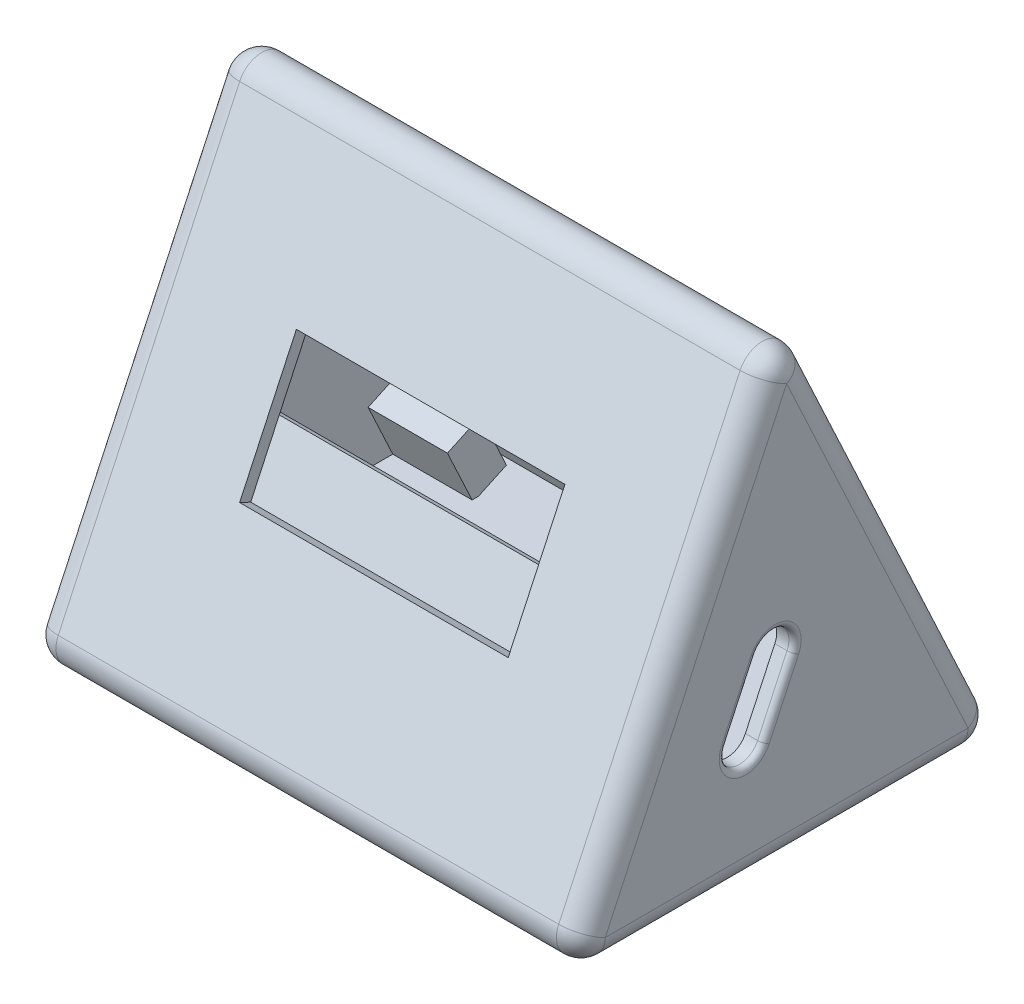
SolidWorks part; units mm, degrees
ref_plane "前视基准面" through (0, 0, 0) normal (0, 0, 1) x (1, 0, 0)
ref_plane "上视基准面" through (0, 0, 0) normal (0, 1, 0) x (1, 0, 0)
ref_plane "右视基准面" through (0, 0, 0) normal (1, 0, 0) x (0, 0, -1)
sketch "草图1" plane through (0, 0, 0) normal (1, 0, 0) x (0, 0, -1)
  line L0 (0, 0) -> (0, 38.6011) construction
  line L1 (18, 0) -> (-18, 0)
  line L2 (-18, 0) -> (0, 38.6011)
  line L3 (18, 0) -> (0, 38.6011)
  dimension "D1" = 18
  dimension "D2" = 65
extrude "凸台-拉伸1" add sketch "草图1" along normal mid plane 45
ref_plane "基准面1" through (0, 6.8944, 14.7851) normal (0, 0.4226, 0.9063) x (1, 0, 0)
sketch "草图2" plane through (0, 6.8944, 14.7851) normal (0, 0.4226, 0.9063) x (1, 0, 0)
  line L0 (0, 37.0396) -> (0, -15.9465) construction
  line L1 (-28.8471, 13.7138) -> (32.5804, 13.7138) construction
  line L2 (-11, 8.2138) -> (11, 8.2138)
  line L3 (11, 8.2138) -> (11, 19.2138)
  line L4 (-11, 19.2138) -> (11, 19.2138)
  line L5 (-11, 8.2138) -> (-11, 19.2138)
  point P9 (11, 13.7138)
  point P11 (0, 8.2138)
  point P12 (0, 19.2138)
  dimension "D1" = 11
  dimension "D2" = 5.5
extrude "切除-拉伸1" cut sketch "草图2" against normal blind 1
ref_plane "基准面2" through (0, 6.4718, 13.8788) normal (0, 0.4226, 0.9063) x (1, 0, 0)
sketch "草图3" plane through (0, 6.4718, 13.8788) normal (0, 0.4226, 0.9063) x (1, 0, 0)
  line L0 (0, 19.8103) -> (0, 5.2367) construction
  line L1 (14, 13.6867) -> (-13.0702, 13.6867) construction
  line L2 (0, 5.2367) -> (14, 5.2367)
  line L3 (14, 5.2367) -> (14, 13.6867)
  line L4 (0, 5.2367) -> (-21, 5.2367)
  line L5 (-21, 5.2367) -> (-21, 28.3584)
  line L6 (-21, 28.3584) -> (14, 28.3584)
  line L7 (14, 28.3584) -> (14, 13.6867)
  line L8 (-22.5, 34.9845) -> (-22.5, -7.6071) construction
  dimension "D1" = 14
  dimension "D2" = 8.45
  dimension "D3" = 1.5
extrude "切除-拉伸2" cut sketch "草图3" against normal blind 1.5
sketch "草图4" plane through (0, 0, 0) normal (1, 0, 0) x (0, 0, -1)
  line L0 (0, 40.4929) -> (0, -2.5128) construction
  line L1 (0.8275, 33.2772) -> (-13.9904, 1.5)
  line L2 (-13.9904, 1.5) -> (15.6455, 1.5)
  line L3 (15.6455, 1.5) -> (0.8275, 33.2772)
  line L4 (0, 38.6011) -> (-18, 0) construction
  line L5 (-18, 0) -> (18, 0) construction
  line L7 (18, 0) -> (0, 38.6011) construction
  dimension "D1" = 3
  dimension "D2" = 1.5
  dimension "D3" = 1.5
extrude "切除-拉伸3" cut sketch "草图4" against normal mid plane 42
ref_plane "基准面3" through (0, 6.8944, -14.7851) normal (0, 0.4226, -0.9063) x (-1, 0, 0)
sketch "草图5" plane through (0, 6.8944, -14.7851) normal (0, 0.4226, -0.9063) x (-1, 0, 0)
  line L0 (0, 37.0585) -> (0, -12.822) construction
  line L1 (-24.7953, 13.7133) -> (25.2303, 13.7133) construction
  line L2 (19.5, -3.6071) -> (-19.5, -3.6071)
  line L3 (-19.5, -3.6071) -> (-19.5, 26.9845)
  line L4 (-19.5, 26.9845) -> (19.5, 26.9845)
  line L5 (-22.5, -7.6071) -> (22.5, -7.6071) construction
  line L6 (-22.5, -7.6071) -> (-22.5, 34.9845) construction
  line L7 (-22.5, 34.9845) -> (22.5, 34.9845) construction
  line L8 (19.5, -3.6071) -> (19.5, 26.9845)
  point P17 (0, -3.6071)
  point P18 (0, 26.9845)
  dimension "D1" = 4
  dimension "D2" = 3
  dimension "D3" = 8
extrude "切除-拉伸4" cut sketch "草图5" against normal blind 1.5
ref_plane "基准面4" through (0, 5.6265, 12.0662) normal (0, -0.4226, -0.9063) x (-1, 0, 0)
sketch "草图6" plane through (0, 5.6265, 12.0662) normal (0, -0.4226, -0.9063) x (-1, 0, 0)
  line L0 (-21, 13.2048) -> (14.1537, 13.2048)
  line L1 (14.1537, 13.2048) -> (14.1537, 10.3593)
  line L2 (14.1537, 10.3593) -> (21, 10.3593)
  line L3 (21, 10.3593) -> (21, 29.9845)
  line L4 (21, 29.9845) -> (-21, 29.9845)
  line L5 (-21, 29.9845) -> (-21, 13.2048)
  line L6 (22.5, 34.9845) -> (22.5, -7.6071) construction
  line L7 (-22.5, 34.9845) -> (22.5, 34.9845) construction
  line L8 (-22.5, 34.9845) -> (-22.5, -7.6071) construction
  dimension "D1" = 1.5
  dimension "D2" = 5
  dimension "D3" = 1.5
extrude "切除-拉伸5" cut sketch "草图6" against normal blind 2
ref_plane "基准面6" through (0, 4.5277, 9.7098) normal (0, -0.4226, -0.9063) x (-1, 0, 0)
sketch "草图9" plane through (0, 4.5277, 9.7098) normal (0, -0.4226, -0.9063) x (-1, 0, 0)
  line L0 (-19.9951, -2.98) -> (-19.9951, 22.2211) construction
  line L1 (-19.9951, 22.2211) -> (19.0049, 22.2211) construction
  line L2 (19.0049, 22.2211) -> (19.0049, -2.98) construction
  line L3 (19.0049, -2.98) -> (-19.9951, -2.98) construction
  line L4 (-22.4951, 30.2673) -> (-22.4951, -4.98) construction
  line L5 (-22.4951, -4.98) -> (22.5177, -4.98) construction
  line L6 (-19.9951, 22.2211) -> (-15.9951, 22.2211)
  line L7 (-15.9951, 22.2211) -> (-15.9951, 18.2211)
  line L8 (-15.9951, 18.2211) -> (-19.9951, 18.2211)
  line L9 (-19.9951, 18.2211) -> (-19.9951, 22.2211)
  line L10 (9.6049, 1.6211) -> (13.6049, 1.6211)
  line L11 (13.6049, 1.6211) -> (13.6049, -2.3789)
  line L12 (13.6049, -2.3789) -> (9.6049, -2.3789)
  line L13 (9.6049, -2.3789) -> (9.6049, 1.6211)
  line L16 (-19.9951, 22.2211) -> (-20.0443, 22.2112) construction
  line L19 (13.6049, -2.3789) -> (13.6019, -2.3862) construction
  dimension "D1" = 2.5
  dimension "D2" = 39
  dimension "D3" = 2
  dimension "D4" = 4
  dimension "D5" = 4
  dimension "D6" = 4
  dimension "D7" = 4
  dimension "D8" = 16.6
  dimension "D9" = 25.6
extrude "凸台-拉伸2" add sketch "草图9" against normal blind 5
sketch "草图10" plane through (0, 4.5277, 9.7098) normal (0, -0.4226, -0.9063) x (-1, 0, 0)
  line L0 (-15.9951, 22.2211) -> (-19.9951, 18.2211) construction
  line L1 (-19.9951, 22.2211) -> (-15.9951, 18.2211) construction
sketch "草图11" plane through (0, 4.5277, 9.7098) normal (0, -0.4226, -0.9063) x (-1, 0, 0)
  line L0 (13.6049, 1.6211) -> (9.6049, -2.3789) construction
  line L1 (9.6049, 1.6211) -> (13.6049, -2.3789) construction
sketch "草图12" plane through (22.5, 0, 0) normal (1, 0, 0) x (0, 0, -1)
  line L2 (-1.164, 22.8542) -> (-5.3056, 13.9724) construction
  line L3 (-4.8583, 14.9317) -> (-3.227, 14.1709) construction
  line L4 (-3.227, 14.1709) -> (-4.9545, 10.4663) construction
  line L5 (-5.3056, 13.9724) -> (1.2067, 10.9357) construction
  line L6 (-3.3734, 9.938) -> (-0.9644, 15.1039) construction
  line L7 (-4.8688, 10.6353) -> (-2.4598, 15.8013)
  line L8 (-1.878, 9.2407) -> (0.531, 14.4066)
  line L9 (-17.5905, -12.3726) -> (-1.829, 21.4281) construction
  arc A0 (-4.8688, 10.6353) -> (-1.878, 9.2407) centre (-3.3734, 9.938) ccw
  arc A1 (0.531, 14.4066) -> (-2.4598, 15.8013) centre (-0.9644, 15.1039) ccw
  point P10 (-2.1689, 12.521)
  point P17 (-4.0707, 8.4426)
  point P18 (-0.2671, 16.5994)
  dimension "D1" = 9.8
  dimension "D2" = 1.8
  dimension "D3" = 3.3
  dimension "D4" = 9
extrude "切除-拉伸6" cut sketch "草图12" against normal blind 5
sketch "草图14" plane through (-22.5, 0, 0) normal (-1, 0, 0) x (0, 0, 1)
  line L4 (-1.12, 30.2837) -> (-3.2331, 25.7522)
  line L5 (-3.2331, 25.7522) -> (-0.5142, 24.4843)
  line L6 (-0.5142, 24.4843) -> (1.5989, 29.0158)
  line L7 (1.5989, 29.0158) -> (-1.12, 30.2837)
  dimension "D2" = 5
  dimension "D3" = 3
extrude "凸台-拉伸3" add sketch "草图14" against normal blind 8
sketch "草图15" plane through (22.5, 0, 0) normal (1, 0, 0) x (0, 0, -1)
  line L4 (14.0438, 2.5687) -> (11.3248, 1.3008)
  line L5 (11.3248, 1.3008) -> (9.2117, 5.8324)
  line L6 (9.2117, 5.8324) -> (11.9307, 7.1002)
  line L7 (11.9307, 7.1002) -> (14.0438, 2.5687)
  dimension "D2" = 5
  dimension "D3" = 3
extrude "凸台-拉伸4" add sketch "草图15" against normal blind 8
sketch "草图18" plane through (0, 5.8379, -12.5193) normal (0, 0.4226, -0.9063) x (-1, 0, 0)
  line L0 (19.5, 26.9845) -> (14.5, 21.973) construction
  line L1 (14.5, 26.973) -> (19.5, 21.973) construction
  line L2 (14.5, 21.973) -> (21, 21.973) construction
  line L3 (19.5, -3.6071) -> (19.5, 26.9845) construction
sketch "草图19" plane through (0, 5.8379, -12.5193) normal (0, 0.4226, -0.9063) x (-1, 0, 0)
  line L0 (-19.5, 1.3929) -> (-14.5, -3.6071) construction
  line L1 (-19.5, 26.9845) -> (-19.5, -3.6071) construction
  line L2 (-14.5, 1.3929) -> (-21, 1.3929) construction
  line L3 (-14.5, 1.3929) -> (-19.5, -3.6071) construction
hole_wizard "M2 螺纹孔3" positions "3D草图4" profile "草图21" tap size "M2" standard "GB"
sketch3d "3D草图4"
  line L0 (-19.5, 30.2941, -1.1152) -> (-14.5, 25.7522, -3.2331) construction
  line L1 (19.5, 7.1002, -11.9307) -> (14.5, 2.5687, -14.0438) construction
  point P0 (17, 4.8345, -12.9872)
  point P2 (-17, 28.0231, -2.1742)
sketch "草图21" plane through (17, 4.8345, -12.9872) normal (1, 0, 0) x (0, 0.9063, 0.4226)
  line L0 (0, 0) -> (0, 2.9807)
  line L1 (0, 2.9807) -> (0.8, 2.5)
  line L2 (0.8, 2.5) -> (0.8, 0)
  line L5 (0.8, 0) -> (0, 0)
  line L10 (0, 2.9807) -> (-0.8, 2.5) construction
  line L11 (0, -6.35) -> (0, 107.95) construction
  dimension "螺纹孔钻头直径" = 1.6
  dimension "螺纹孔钻头深度" = 2.5
  dimension "导头角度" = 118
cosmetic thread "孔螺蚊线7" parameters "D1"=2.3, "D2"=2
cosmetic thread "孔螺蚊线8" parameters "D1"=2.3, "D2"=2
hole_wizard "M2 螺纹孔5" positions "3D草图6" profile "草图23" tap size "M2" standard "GB"
sketch3d "3D草图6"
  line L0 (15.9951, 24.6669, 0.3187) -> (19.9951, 21.0416, 2.0092) construction
  point P0 (17.9951, 22.8542, 1.164)
  point P5 (17.9951, 22.8542, 1.164)
  point P6 (17.9951, 22.8542, 1.164)
sketch "草图23" plane through (17.9951, 22.8542, 1.164) normal (1, 0, 0) x (0, 0.9063, -0.4226)
  line L0 (0, 0) -> (0, 2.9807)
  line L1 (0, 2.9807) -> (0.8, 2.5)
  line L2 (0.8, 2.5) -> (0.8, 0)
  line L5 (0.8, 0) -> (0, 0)
  line L10 (0, 2.9807) -> (-0.8, 2.5) construction
  line L11 (0, -6.35) -> (0, 107.95) construction
  dimension "螺纹孔钻头直径" = 1.6
  dimension "螺纹孔钻头深度" = 2.5
  dimension "导头角度" = 118
cosmetic thread "孔螺蚊线11" parameters "D1"=2.3, "D2"=2
cosmetic thread "孔螺蚊线12" parameters "D1"=2.3, "D2"=2
ref_plane "基准面7" through (0, 0, 9) normal (0, 0, 1) x (1, 0, 0)
sketch "草图27" plane through (-22.5, 0, 0) normal (-1, 0, 0) x (0, 0, 1)
  line L4 (-14.9501, 2.9913) -> (-12.2711, 1.7421) construction
  line L5 (-14.0438, 2.5687) -> (-11.9307, 7.1002)
  line L6 (-11.9307, 7.1002) -> (-9.2117, 5.8324)
  line L7 (-9.2117, 5.8324) -> (-11.3248, 1.3008)
  line L8 (-11.3248, 1.3008) -> (-14.0438, 2.5687)
  dimension "D2" = 3
  dimension "D3" = 5
extrude "凸台-拉伸6" add sketch "草图27" against normal blind 8
sketch "草图28" plane through (22.5, 0, 0) normal (1, 0, 0) x (0, 0, -1)
  line L4 (2.0215, 30.7167) -> (-1.2539, 29.1894) construction
  line L5 (1.1152, 30.2941) -> (-1.6037, 29.0263)
  line L6 (-1.6037, 29.0263) -> (0.5093, 24.4947)
  line L7 (0.5093, 24.4947) -> (3.2283, 25.7626)
  line L9 (1.1152, 30.2941) -> (3.2283, 25.7626)
  dimension "D2" = 5
  dimension "D3" = 3
extrude "凸台-拉伸7" add sketch "草图28" against normal blind 8
sketch "草图29" plane through (0, 5.8379, -12.5193) normal (0, 0.4226, -0.9063) x (-1, 0, 0)
  line L0 (-14.5, 21.9845) -> (-19.5, 26.9845) construction
  line L1 (-14.5, 26.9845) -> (-19.5, 21.9845) construction
  line L2 (-19.5, 26.9845) -> (-19.5, -3.6071) construction
  line L3 (-14.5, 21.9845) -> (-21, 21.9845) construction
sketch "草图31" plane through (0, 5.8379, -12.5193) normal (0, 0.4226, -0.9063) x (-1, 0, 0)
  line L0 (19.5, -3.6071) -> (14.5, 1.3929) construction
  line L1 (14.5, 1.3929) -> (14.5, -3.6071) construction
  line L2 (19.5, 1.3929) -> (14.5, -3.6071) construction
  line L3 (14.5, 1.3929) -> (21, 1.3929) construction
  line L4 (19.5, -3.6071) -> (19.5, 26.9845) construction
hole_wizard "M2 螺纹孔7" positions "3D草图8" profile "草图32" tap size "M2" standard "GB"
sketch3d "3D草图8"
  line L0 (14.5, 25.7626, -3.2283) -> (19.5, 30.2941, -1.1152) construction
  line L1 (-19.5, 2.5687, -14.0438) -> (-14.5, 7.1002, -11.9307) construction
  point P0 (17, 28.0283, -2.1717)
  point P2 (-17, 4.8345, -12.9872)
  point P3 (17, 28.0283, -2.1717)
  point P6 (-17, 4.8345, -12.9872)
sketch "草图32" plane through (17, 28.0283, -2.1717) normal (1, 0, 0) x (0, 0.9063, 0.4226)
  line L0 (0, 0) -> (0, 2.9807)
  line L1 (0, 2.9807) -> (0.8, 2.5)
  line L2 (0.8, 2.5) -> (0.8, 0)
  line L5 (0.8, 0) -> (0, 0)
  line L10 (0, 2.9807) -> (-0.8, 2.5) construction
  line L11 (0, -6.35) -> (0, 107.95) construction
  dimension "螺纹孔钻头直径" = 1.6
  dimension "螺纹孔钻头深度" = 2.5
  dimension "导头角度" = 118
cosmetic thread "孔螺蚊线14" parameters "D1"=2.5, "D2"=2
cosmetic thread "孔螺蚊线15" parameters "D1"=2.5, "D2"=2
hole_wizard "M2 螺纹孔11" positions "草图36" profile "草图35" tap size "M2" standard "GB"
sketch "草图36" plane through (0, 0, 9) normal (0, 0, 1) x (1, 0, 0)
  line L0 (-13.6049, 5.9969) -> (-9.6049, 2.3717) construction
  point P4 (-11.6049, 4.1843)
  point P7 (0, 0)
  point P8 (0, 0)
  point P9 (-11.6098, 4.627)
  point P10 (-11.5983, 4.0551)
  point P11 (-11.6299, 4.1348)
  point P12 (-11.6795, 4.0438)
  point P13 (0, 0)
  point P14 (-11.6049, 4.1843)
  point P17 (0, 0)
sketch "草图35" plane through (-11.6049, 4.1843, 9) normal (1, 0, 0) x (0, 1, 0)
  line L0 (0, 0) -> (0, 3.4807)
  line L1 (0, 3.4807) -> (0.8, 3)
  line L2 (0.8, 3) -> (0.8, 0)
  line L5 (0.8, 0) -> (0, 0)
  line L10 (0, 3.4807) -> (-0.8, 3) construction
  line L11 (0, -6.35) -> (0, 107.95) construction
  dimension "螺纹孔钻头直径" = 1.6
  dimension "螺纹孔钻头深度" = 3
  dimension "导头角度" = 118
cosmetic thread "孔螺蚊线16" parameters "D1"=2.8, "D2"=2
fillet "圆角2" radius 2 9 edges at (-22.5, 0, 0) (0, 0, -18) (22.5, 0, 0) (0, 0, 18) (-22.5, 19.3006, 9) (-22.5, 19.3006, -9) (0, 38.6011, 0) (22.5, 19.3006, 9) (22.5, 19.3006, -9)
fillet "圆角3" radius 0.5 4 edges at (22.5, 13.2183, 3.6643) (22.5, 16.5994, 0.2671) (22.5, 11.8237, 0.6735) (22.5, 8.4426, 4.0707)
